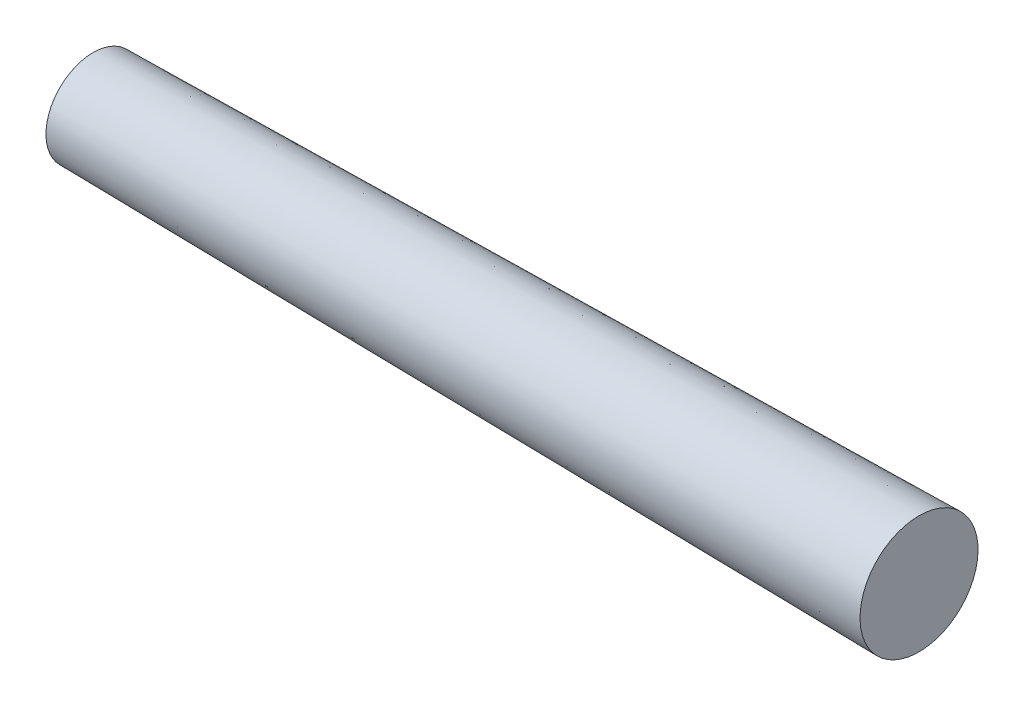
SolidWorks part; units mm, degrees
ref_plane "Front Plane" through (0, 0, 0) normal (0, 0, 1) x (1, 0, 0)
ref_plane "Top Plane" through (0, 0, 0) normal (0, 1, 0) x (1, 0, 0)
ref_plane "Right Plane" through (0, 0, 0) normal (1, 0, 0) x (0, 0, -1)
sketch "Sketch1" plane through (0, 0, 0) normal (0, 0, 1) x (1, 0, 0)
  line L0 (0, 0) -> (0, 2)
  line L1 (0, 2) -> (35, 2.5)
  line L2 (35, 2.5) -> (35, 0)
  line L3 (35, 0) -> (0, 0)
  dimension "D1" = 2
  dimension "D2" = 2.5
  dimension "D3" = 35
revolve "Revolve1" add sketch "Sketch1" angle 360 about L3
